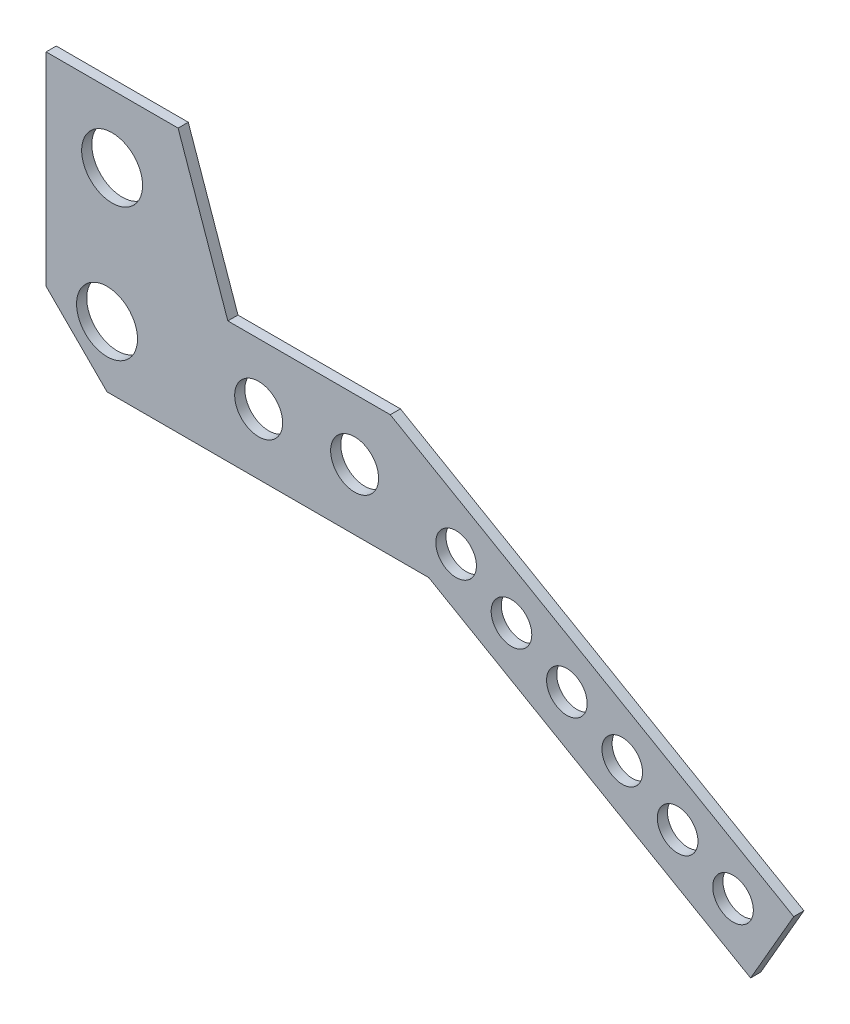
SolidWorks part; units mm, degrees
ref_plane "Front Plane" through (0, 0, 0) normal (0, 0, 1) x (1, 0, 0)
ref_plane "Top Plane" through (0, 0, 0) normal (0, 1, 0) x (1, 0, 0)
ref_plane "Right Plane" through (0, 0, 0) normal (1, 0, 0) x (0, 0, -1)
sketch "Sketch2" plane through (0, 0, 0) normal (0, 0, 1) x (1, 0, 0)
  line L1 (-19.05, 82.55) -> (22.225, 82.55)
  line L2 (22.225, 82.55) -> (37.7757, 38.1)
  line L3 (37.7757, 38.1) -> (88.5757, 38.1)
  line L6 (201.2413, -58.11) -> (100.5918, 0)
  line L7 (100.5918, 0) -> (0, 0)
  line L8 (0, 0) -> (-19.05, 19.05)
  line L9 (-19.05, 19.05) -> (-19.05, 82.55)
  line L10 (88.5757, 38.1) -> (214.7351, -34.7382)
  line L12 (207.9882, -46.4241) -> (109.1511, 10.6395) construction
  line L13 (214.7351, -34.7382) -> (201.2413, -58.11)
  line L16 (115.898, 22.3254) -> (102.4043, -1.0464) construction
  line L17 (47.4154, 38.1) -> (47.4154, 0) construction
  circle A0 centre (109.1511, 10.6395) radius 6.35
  circle A1 centre (126.4716, 0.6395) radius 6.35
  circle A2 centre (143.7921, -9.3605) radius 6.35
  circle A3 centre (161.1127, -19.3605) radius 6.35
  circle A4 centre (178.4332, -29.3605) radius 6.35
  circle A5 centre (195.7537, -39.3605) radius 6.35
  circle A6 centre (47.4154, 19.05) radius 7.5
  circle A7 centre (77.4154, 19.05) radius 7.5
  circle A8 centre (0, 19.05) radius 9.525
  circle A9 centre (1.5875, 61.4462) radius 9.525
  point P36 (1.5875, 82.55)
  dimension "D7" = 12.7
  dimension "D15" = 15
  dimension "D16" = 15
  dimension "D18" = 19.05
  dimension "D1" = 41.275
  dimension "D2" = 50.8
  dimension "D3" = 63.5
  dimension "D4" = 19.05
  dimension "D5" = 135
  dimension "D6" = 38.1
  dimension "D8" = 20
  dimension "D9" = 20
  dimension "D10" = 20
  dimension "D11" = 20
  dimension "D12" = 20
  dimension "D13" = 150
  dimension "D14" = 26.9875
  dimension "D17" = 30
  dimension "D19" = 19.05
  dimension "D20" = 19.05
extrude "Boss-Extrude1" add sketch "Sketch2" along normal blind 3.175
